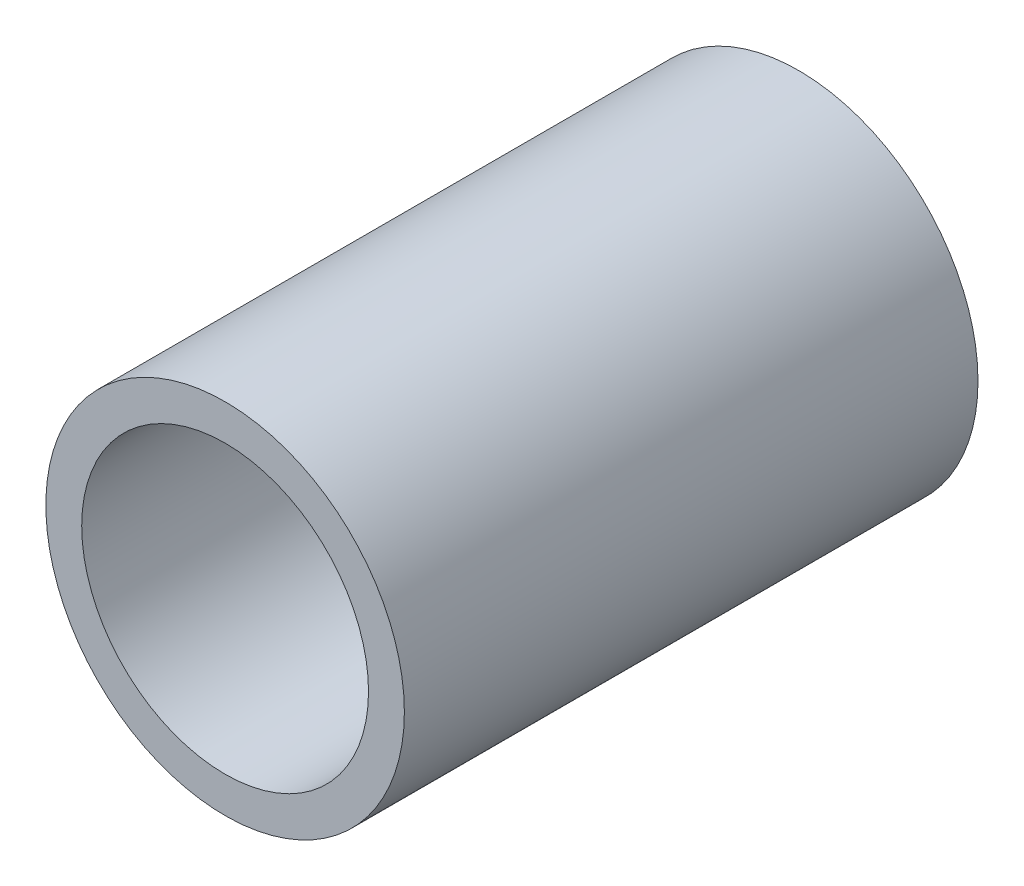
SolidWorks part; units mm, degrees
ref_plane "Front Plane" through (0, 0, 0) normal (0, 0, 1) x (1, 0, 0)
ref_plane "Top Plane" through (0, 0, 0) normal (0, 1, 0) x (1, 0, 0)
ref_plane "Right Plane" through (0, 0, 0) normal (1, 0, 0) x (0, 0, -1)
sketch "Sketch1" plane through (0, 0, 0) normal (0, 0, 1) x (1, 0, 0)
  circle A0 centre (0, 0) radius 6
  circle A1 centre (0, 0) radius 7.5
  dimension "D1" = 12
  dimension "D2" = 15
extrude "Boss-Extrude1" add sketch "Sketch1" along normal mid plane 24
